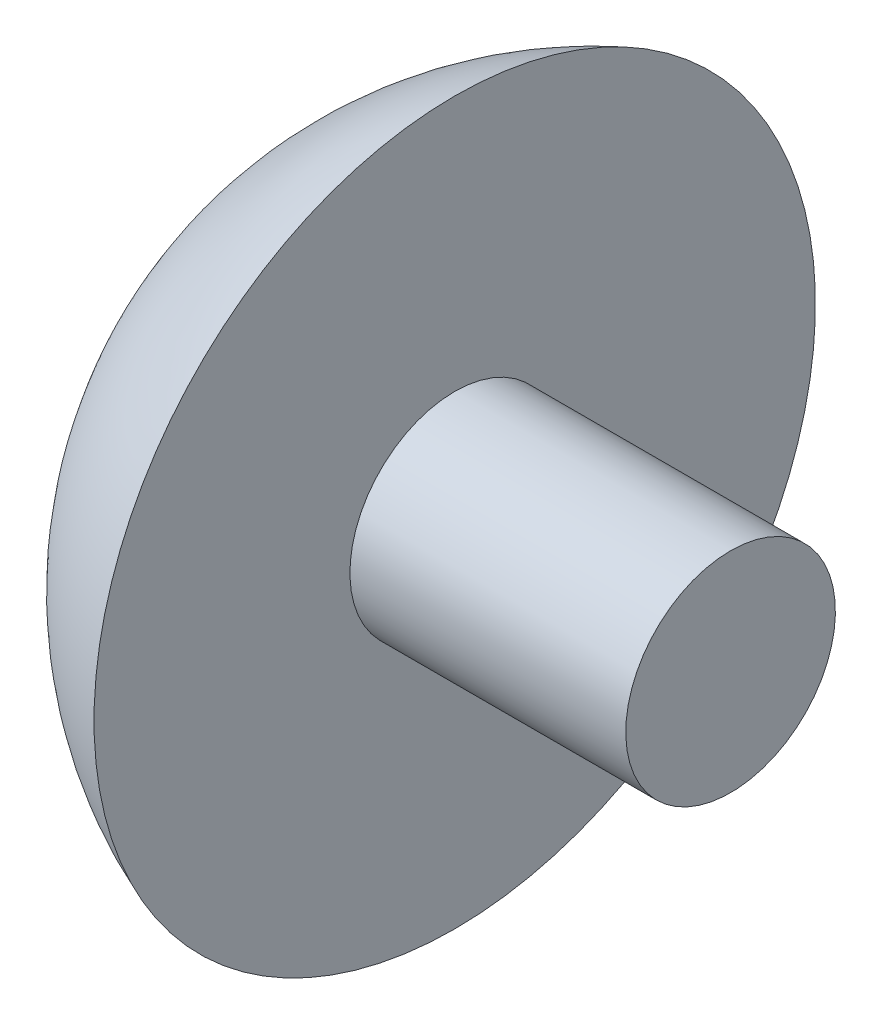
SolidWorks part; units mm, degrees
ref_plane "Plan de face" through (0, 0, 0) normal (0, 0, 1) x (1, 0, 0)
ref_plane "Plan de dessus" through (0, 0, 0) normal (0, 1, 0) x (1, 0, 0)
ref_plane "Plan de droite" through (0, 0, 0) normal (1, 0, 0) x (0, 0, -1)
sketch "Esquisse5" plane through (0, 0, 0) normal (0, 0, 1) x (1, 0, 0)
  line L0 (0, 0) -> (-9.5, 0)
  line L1 (0, 0) -> (0, -1.9)
  line L2 (0, -1.9) -> (-5, -1.9)
  line L3 (-5, -1.9) -> (-5, -6.5383)
  arc A0 (-9.5, 0) -> (-5, -6.5383) centre (-2.5, 0) ccw
  dimension "D1" = 7
  dimension "D2" = 9.5
  dimension "D3" = 1.9
  dimension "D4" = 5
revolve "Révolution2" add sketch "Esquisse5" angle 360 about L0
